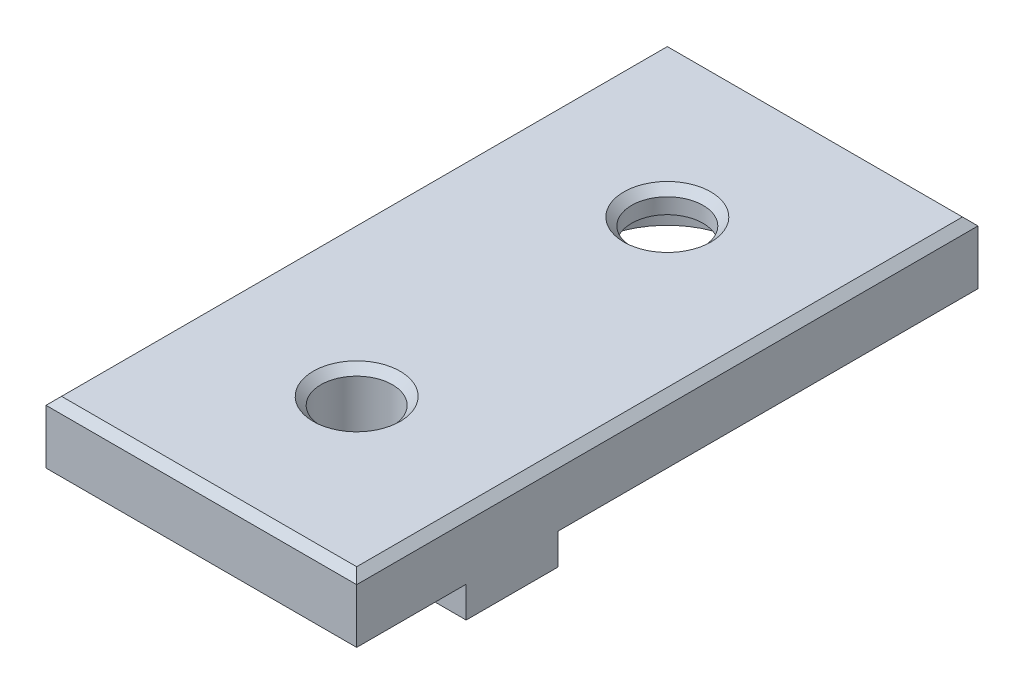
SolidWorks part; units mm, degrees
ref_plane "Plano frontal" through (0, 0, 0) normal (0, 0, 1) x (1, 0, 0)
ref_plane "Plano superior" through (0, 0, 0) normal (0, 1, 0) x (1, 0, 0)
ref_plane "Plano direito" through (0, 0, 0) normal (1, 0, 0) x (0, 0, -1)
sketch "Esboço1" plane through (0, 0, 0) normal (0, 1, 0) x (1, 0, 0)
  line L1 (-10, 20) -> (10, 20)
  line L2 (-10, 20) -> (-10, -20)
  line L3 (-10, -20) -> (10, -20)
  line L4 (10, 20) -> (10, -20)
  line L5 (-10, 20) -> (10, -20) construction
  line L6 (-10, -20) -> (10, 20) construction
  point P0 (0, 0)
  dimension "D1" = 20
  dimension "D2" = 40
extrude "Ressalto-extrusão1" add sketch "Esboço1" along normal blind 4
sketch "Esboço2" plane through (0, 4, 0) normal (0, 1, 0) x (1, 0, 0)
  line L0 (-10, 0) -> (10, 0) construction
  line L1 (-10, -20) -> (10, -20) construction
  line L2 (10, -20) -> (10, 20) construction
  line L5 (-10, 20) -> (-10, -20) construction
  line L6 (10, -20) -> (10, 20) construction
  line L7 (10, 20) -> (-10, 20) construction
  circle A0 centre (0, 10) radius 2.3
  circle A1 centre (0, -10) radius 2.3
  dimension "D1" = 4.6
  dimension "D2" = 4.6
  dimension "D3" = 10
  dimension "D4" = 10
  dimension "D5" = 10
extrude "Corte-extrusão1" cut sketch "Esboço2" against normal through all both and the other way through all
sketch "Esboço3" plane through (0, 0, 0) normal (0, -1, 0) x (1, 0, 0)
  line L0 (-10, 0) -> (10, 0) construction
  line L1 (-2.95, -7) -> (2.95, -7)
  line L2 (-2.95, -7) -> (-2.95, -1)
  line L3 (-2.95, -1) -> (2.95, -1)
  line L4 (2.95, -7) -> (2.95, -1)
  line L5 (-2.95, -7) -> (2.95, -1) construction
  line L6 (-2.95, -1) -> (2.95, -7) construction
  line L7 (-2.95, -13) -> (2.95, -13)
  line L8 (-2.95, -13) -> (-2.95, -20)
  line L9 (-2.95, -20) -> (2.95, -20)
  line L10 (2.95, -13) -> (2.95, -20)
  line L11 (-2.95, -13) -> (2.95, -20) construction
  line L12 (-2.95, -20) -> (2.95, -13) construction
  line L13 (-10, 12.95) -> (-3, 12.95)
  line L14 (-10, 12.95) -> (-10, 7.05)
  line L15 (-10, 7.05) -> (-3, 7.05)
  line L16 (-3, 12.95) -> (-3, 7.05)
  line L17 (-10, 12.95) -> (-3, 7.05) construction
  line L18 (-10, 7.05) -> (-3, 12.95) construction
  line L19 (3, 12.95) -> (10, 12.95)
  line L20 (3, 12.95) -> (3, 7.05)
  line L21 (3, 7.05) -> (10, 7.05)
  line L22 (10, 12.95) -> (10, 7.05)
  line L23 (3, 12.95) -> (10, 7.05) construction
  line L24 (3, 7.05) -> (10, 12.95) construction
  line L26 (-10, -20) -> (-10, 20) construction
  line L29 (10, 20) -> (10, -20) construction
  line L30 (10, -20) -> (-10, -20) construction
  circle A1 centre (0, -10) radius 2.3 construction
  circle A2 centre (0, 10) radius 2.3 construction
  point P0 (0, -4)
  point P5 (0, -16.5)
  point P10 (-6.5, 10)
  point P15 (6.5, 10)
  point P20 (0, 10)
  point P23 (0, -10)
  point P28 (0, -13)
  line M28 (10, -20) -> (10, 20)
  line M30 (-10, 20) -> (-10, -20)
  dimension "D2" = 5.9
  dimension "D3" = 5.9
  dimension "D4" = 5.9
  dimension "D5" = 5.9
  dimension "D6" = 1
  dimension "D1" = 3
  dimension "D7" = 3
  dimension "D8" = 3
  dimension "D9" = 3
extrude "Ressalto-extrusão2" add sketch "Esboço3" along normal blind 2 contours L20 L21 L19 M28 | L16 L13 L15 M30
chamfer "Chanfro1" distance 0.5 angle 45 6 edges at (0, 4, 20) (-10, 4, 0) (0, 4, -20) (10, 4, 0) (0, 4, -7.7) (0, 4, 12.3)
sketch "Esboço4" plane through (0, 0, 0) normal (0, -1, 0) x (1, 0, 0)
  circle A0 centre (0, -10) radius 5
  dimension "D1" = 10
extrude "Corte-extrusão2" cut sketch "Esboço4" against normal blind 2.5
equation "\"D3@Esboço3\"=\"D2@Esboço3\""
equation "\"D4@Esboço3\"=\"D2@Esboço3\""
equation "\"D1@Esboço2\"=\"D2@Esboço2\""
equation "\"D8@Esboço3\"=\"D1@Esboço3\""
equation "\"D9@Esboço3\"=\"D1@Esboço3\""
